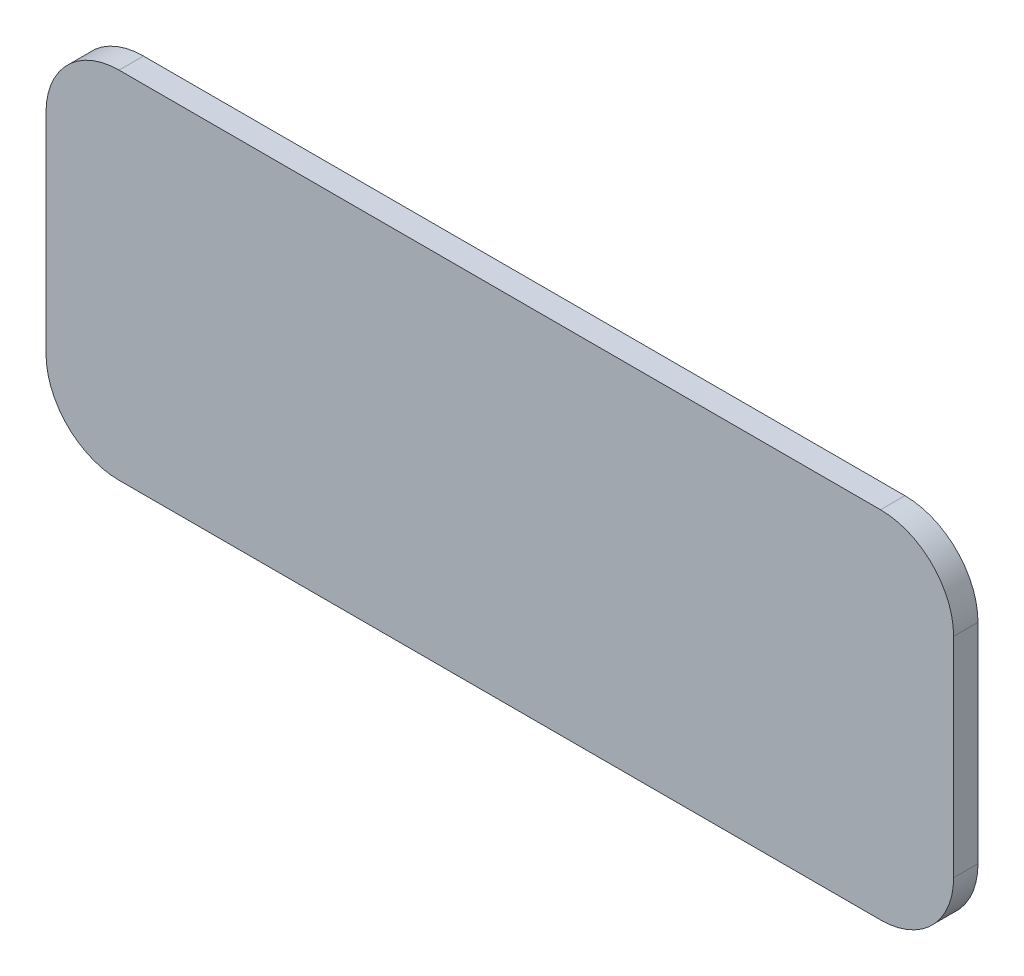
SolidWorks part; units mm, degrees
material "PC High Viscosity"
ref_plane "Front Plane" through (0, 0, 0) normal (0, 0, 1) x (1, 0, 0)
ref_plane "Top Plane" through (0, 0, 0) normal (0, 1, 0) x (1, 0, 0)
ref_plane "Right Plane" through (0, 0, 0) normal (1, 0, 0) x (0, 0, -1)
sketch "Sketch1" plane through (0, 0, 0) normal (0, 0, 1) x (1, 0, 0)
  line L0 (-268.5, -17.5) -> (-268.5, 33.9825)
  line L1 (-268.5, 33.9825) -> (-268.5, -17.5) construction
  line L2 (-250.5, 51.9825) -> (-62.9918, 51.9825)
  line L3 (-44.9918, 33.9825) -> (-44.9918, -17.5)
  line L4 (-62.9918, -35.5) -> (-250.5, -35.5)
  line L5 (-250.5, -35.5) -> (-62.9918, -35.5) construction
  arc A0 (-250.5, 51.9825) -> (-268.5, 33.9825) centre (-250.5, 33.9825) ccw construction
  arc A1 (-268.5, 33.9825) -> (-250.5, 51.9825) centre (-250.5, 33.9825) cw
  arc A2 (-62.9918, 51.9825) -> (-44.9918, 33.9825) centre (-62.9918, 33.9825) cw
  arc A3 (-44.9918, -17.5) -> (-62.9918, -35.5) centre (-62.9918, -17.5) cw
  arc A4 (-268.5, -17.5) -> (-250.5, -35.5) centre (-250.5, -17.5) ccw construction
  arc A5 (-250.5, -35.5) -> (-268.5, -17.5) centre (-250.5, -17.5) cw
extrude "Boss-Extrude1" add sketch "Sketch1" along normal blind 6
